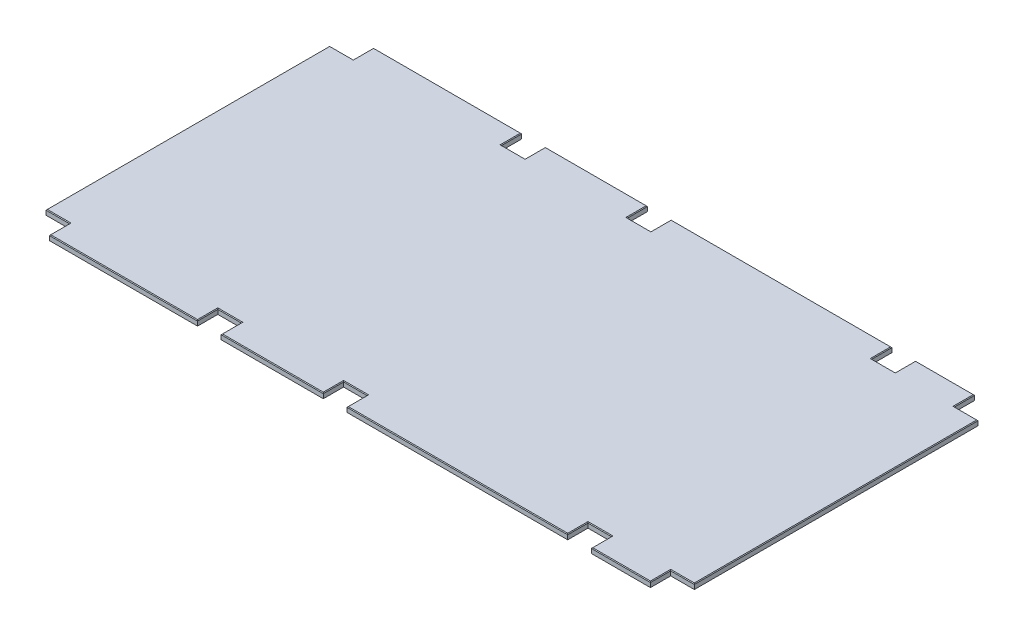
SolidWorks part; units mm, degrees
material "Oak"
ref_plane "Front Plane" through (0, 0, 0) normal (0, 0, 1) x (1, 0, 0)
ref_plane "Top Plane" through (0, 0, 0) normal (0, 1, 0) x (1, 0, 0)
ref_plane "Right Plane" through (0, 0, 0) normal (1, 0, 0) x (0, 0, -1)
sketch "Sketch1" plane through (0, 0, 0) normal (0, 1, 0) x (1, 0, 0)
  line L1 (0, 1219.2) -> (2438.4, 1219.2)
  line L2 (0, 1219.2) -> (0, 0)
  line L3 (0, 0) -> (2438.4, 0)
  line L4 (2438.4, 1219.2) -> (2438.4, 0)
  dimension "D1" = 1219.2
  dimension "D2" = 2438.4
extrude "Boss-Extrude1" add sketch "Sketch1" along normal mid plane 19.05
sketch "Sketch2" plane through (0, 9.525, 0) normal (0, 1, 0) x (1, 0, 0)
  line L5 (2438.4, 1219.2) -> (0, 1219.2) construction
  line L7 (0, 1219.2) -> (88.9, 1219.2)
  line L8 (0, 1219.2) -> (0, 1143)
  line L9 (0, 1143) -> (88.9, 1143)
  line L10 (88.9, 1219.2) -> (88.9, 1143)
  line L11 (646.1125, 1219.2) -> (735.0125, 1219.2)
  line L12 (646.1125, 1219.2) -> (646.1125, 1143)
  line L13 (646.1125, 1143) -> (735.0125, 1143)
  line L15 (2438.4, 0) -> (2438.4, 1219.2) construction
  line L18 (1119.1875, 1143) -> (1208.0875, 1143)
  line L19 (1208.0875, 1219.2) -> (1208.0875, 1143)
  line L20 (2038.35, 1219.2) -> (2127.25, 1219.2)
  line L21 (2038.35, 1219.2) -> (2038.35, 1143)
  line L22 (2038.35, 1143) -> (2127.25, 1143)
  line L23 (2127.25, 1219.2) -> (2127.25, 1143)
  line L24 (2349.5, 1219.2) -> (2438.4, 1219.2)
  line L25 (2349.5, 1219.2) -> (2349.5, 1143)
  line L26 (2349.5, 1143) -> (2438.4, 1143)
  line L27 (2438.4, 1219.2) -> (2438.4, 1143)
  line L28 (735.0125, 1219.2) -> (735.0125, 1143)
  line L29 (0, 1219.2) -> (0, 0) construction
  line L30 (1208.0875, 1219.2) -> (1119.1875, 1219.2)
  line L31 (1119.1875, 1219.2) -> (1119.1875, 1143)
  line L32 (0, 609.6) -> (2438.4, 609.6) construction
  line L33 (1119.1875, 0) -> (1119.1875, 76.2)
  line L34 (1208.0875, 0) -> (1119.1875, 0)
  line L35 (735.0125, 0) -> (735.0125, 76.2)
  line L36 (2438.4, 0) -> (2438.4, 76.2)
  line L37 (2349.5, 76.2) -> (2438.4, 76.2)
  line L38 (2349.5, 0) -> (2349.5, 76.2)
  line L39 (2349.5, 0) -> (2438.4, 0)
  line L40 (2127.25, 0) -> (2127.25, 76.2)
  line L41 (2038.35, 76.2) -> (2127.25, 76.2)
  line L42 (2038.35, 0) -> (2038.35, 76.2)
  line L43 (2038.35, 0) -> (2127.25, 0)
  line L44 (1208.0875, 0) -> (1208.0875, 76.2)
  line L45 (1119.1875, 76.2) -> (1208.0875, 76.2)
  line L46 (646.1125, 76.2) -> (735.0125, 76.2)
  line L47 (646.1125, 0) -> (646.1125, 76.2)
  line L48 (646.1125, 0) -> (735.0125, 0)
  line L49 (88.9, 0) -> (88.9, 76.2)
  line L50 (0, 76.2) -> (88.9, 76.2)
  line L51 (0, 0) -> (0, 76.2)
  line L52 (0, 0) -> (88.9, 0)
  point P25 (0, 1181.1)
  point P27 (1208.0875, 1181.1)
  dimension "D1" = 76.2
  dimension "D2" = 88.9
  dimension "D3" = 646.1125
  dimension "D4" = 735.0125
  dimension "D5" = 88.9
  dimension "D6" = 311.15
  dimension "D7" = 400.05
  dimension "D8" = 830.2625
  dimension "D9" = 88.9
extrude "Cut-Extrude1" cut sketch "Sketch2" against normal through all
chamfer "Chamfer1" distance 2.54 angle 45 36 edges at (0, 9.525, -609.6) (44.45, 9.525, -1143) (88.9, 9.525, -1181.1) (367.5062, 9.525, -1219.2) (646.1125, 9.525, -1181.1) (690.5625, 9.525, -1143) (735.0125, 9.525, -1181.1) (927.1, 9.525, -1219.2) (1119.1875, 9.525, -1181.1) (1163.6375, 9.525, -1143) (1208.0875, 9.525, -1181.1) (1623.2188, 9.525, -1219.2) (2038.35, 9.525, -1181.1) (2082.8, 9.525, -1143) (2127.25, 9.525, -1181.1) (2238.375, 9.525, -1219.2) (2349.5, 9.525, -1181.1) (2393.95, 9.525, -1143) (2438.4, 9.525, -609.6) (2393.95, 9.525, -76.2) (2349.5, 9.525, -38.1) (2238.375, 9.525, 0) (2127.25, 9.525, -38.1) (2082.8, 9.525, -76.2) (2038.35, 9.525, -38.1) (1623.2187, 9.525, 0) (1208.0875, 9.525, -38.1) (1163.6375, 9.525, -76.2) (1119.1875, 9.525, -38.1) (927.1, 9.525, 0) (735.0125, 9.525, -38.1) (690.5625, 9.525, -76.2) (646.1125, 9.525, -38.1) (367.5062, 9.525, 0) (88.9, 9.525, -38.1) (44.45, 9.525, -76.2)
